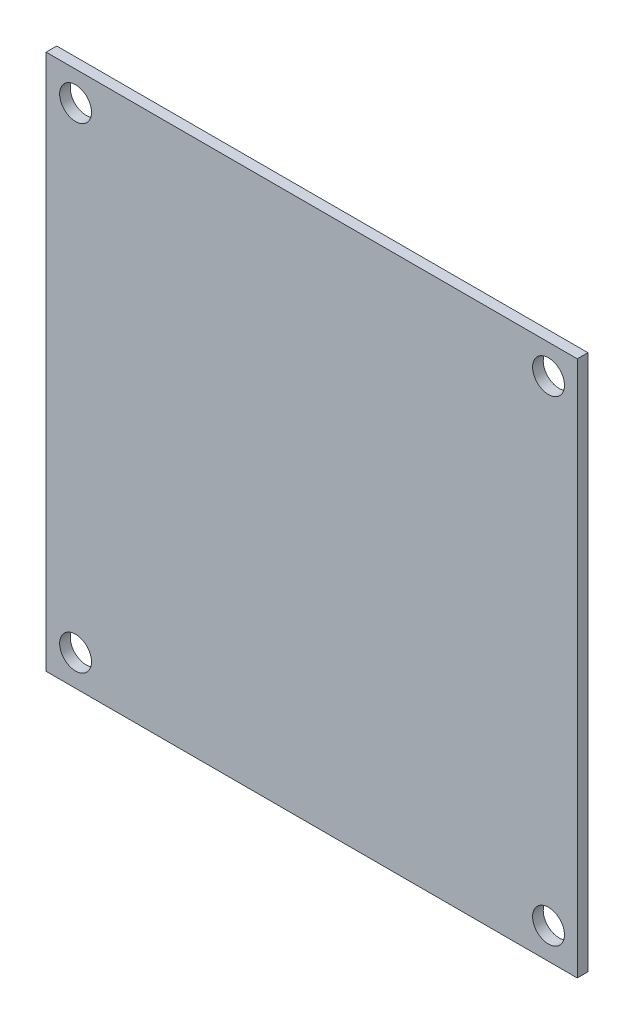
SolidWorks part; units mm, degrees
ref_plane "Front Plane" through (0, 0, 0) normal (0, 0, 1) x (1, 0, 0)
ref_plane "Top Plane" through (0, 0, 0) normal (0, 1, 0) x (1, 0, 0)
ref_plane "Right Plane" through (0, 0, 0) normal (1, 0, 0) x (0, 0, -1)
sketch "Sketch2" plane through (0, 0, 0) normal (0, 0, 1) x (1, 0, 0)
  line L1 (25, 40) -> (-25, 40)
  line L2 (25, 40) -> (25, -40)
  line L3 (25, -40) -> (-25, -40)
  line L4 (-25, 40) -> (-25, -40)
  line L5 (25, 40) -> (-25, -40) construction
  line L6 (25, -40) -> (-25, 40) construction
  point P0 (0, 0)
  dimension "D1" = 80
  dimension "D2" = 50
extrude "Boss-Extrude1" add sketch "Sketch2" along normal blind 1
sketch "Sketch3" plane through (0, 0, 0) normal (0, 0, -1) x (-1, 0, 0)
  line L0 (25, 10.4808) -> (-25, 10.4808)
  line L1 (25, 40) -> (25, -40) construction
  line L2 (-25, -40) -> (-25, 40) construction
  line L3 (-25, 10.4808) -> (-25, 40)
  line L4 (-25, 40) -> (25, 40)
  line L5 (25, 40) -> (25, 10.4808)
extrude "Cut-Extrude1" cut sketch "Sketch3" against normal blind 1
sketch "Sketch4" plane through (0, 0, 0) normal (0, 0, -1) x (-1, 0, 0)
  circle A0 centre (-22.2956, 7.7083) radius 1.5
  circle A1 centre (-22.2956, -37.0896) radius 1.5
  circle A2 centre (22.2267, 7.7083) radius 1.5
  circle A3 centre (22.2267, -37.0896) radius 1.5
  dimension "D1" = 3
  dimension "D2" = 3
  dimension "D3" = 3
  dimension "D4" = 3
extrude "Cut-Extrude2" cut sketch "Sketch4" against normal blind 1
